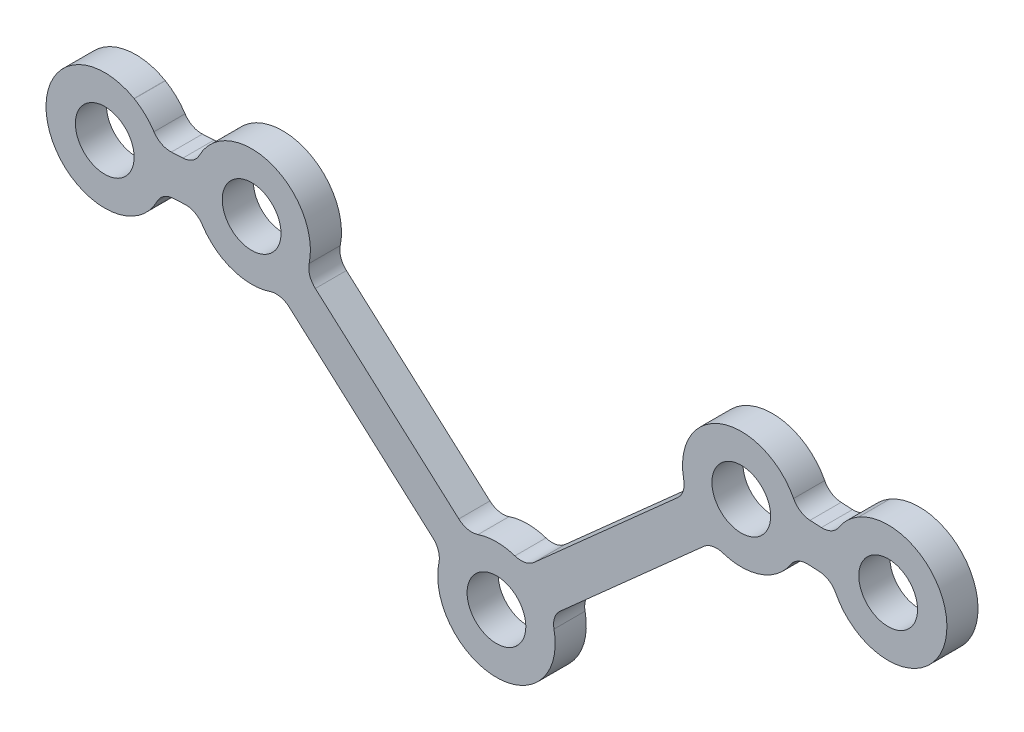
SolidWorks part; units mm, degrees
ref_plane "Front Plane" through (0, 0, 0) normal (0, 0, 1) x (1, 0, 0)
ref_plane "Top Plane" through (0, 0, 0) normal (0, 1, 0) x (1, 0, 0)
ref_plane "Right Plane" through (0, 0, 0) normal (1, 0, 0) x (0, 0, -1)
sketch "Sketch4" plane through (0, 0, 0) normal (0, 0, 1) x (1, 0, 0)
  line L0 (0, -3) -> (0, 1.5) construction
  line L6 (11, 11.1368) -> (10.9965, 11.1337)
  line L7 (-1.9217, 3.0508) -> (-9.2481, 9.5764)
  line L8 (-16.5994, 11.9343) -> (-16.0088, 11.9632)
  line L9 (-10.9965, 11.1337) -> (-11, 11.1368)
  line L10 (10.5783, 8.0829) -> (3.2519, 1.5573)
  line L11 (-3.2519, 1.5573) -> (-10.5783, 8.0829)
  line L12 (-16.4824, 9.9376) -> (-15.9111, 9.9656)
  line L13 (16.5915, 11.9257) -> (16.0107, 11.9554)
  line L16 (0, -3) -> (0, 1.5) construction
  line L19 (-10.9965, 11.1337) -> (-11, 11.1337) construction
  line L26 (10.9965, 11.1337) -> (11, 11.1337) construction
  line L27 (9.2481, 9.5764) -> (1.9217, 3.0508)
  line L28 (16.4893, 9.9283) -> (15.9085, 9.958)
  arc A0 (0.9424, 2.8481) -> (-0.9424, 2.8481) centre (0, 0) ccw
  circle A1 centre (-12.5, 11.1337) radius 1.5
  circle A2 centre (-20, 10.75) radius 1.5
  arc A3 (17.3287, 9.3847) -> (17.482, 12.3808) centre (20, 10.75) ccw
  arc A4 (-17.4862, 12.3873) -> (-17.3252, 9.3916) centre (-20, 10.75) ccw
  arc A5 (15.1713, 12.499) -> (9.5622, 10.5258) centre (12.5, 11.1337) ccw
  arc A6 (-9.5622, 10.5258) -> (-15.1683, 12.5049) centre (-12.5, 11.1337) ccw
  arc A7 (11.5576, 8.2856) -> (15.018, 9.5029) centre (12.5, 11.1337) ccw
  arc A8 (-2.9378, 0.6079) -> (2.9378, 0.6079) centre (0, 0) ccw
  arc A9 (-15.0217, 9.5085) -> (-11.5576, 8.2856) centre (-12.5, 11.1337) ccw
  arc A10 (17.482, 12.3808) -> (16.5915, 11.9257) centre (16.6426, 12.9244) cw
  arc A11 (15.1713, 12.499) -> (16.0107, 11.9554) centre (16.0618, 12.9541) ccw
  arc A12 (17.3287, 9.3847) -> (16.4893, 9.9283) centre (16.4382, 8.9296) ccw
  arc A13 (15.018, 9.5029) -> (15.9085, 9.958) centre (15.8574, 8.9593) cw
  circle A14 centre (0, 0) radius 1.5
  arc A15 (10.5783, 8.0829) -> (11.5576, 8.2856) centre (11.2435, 7.3362) cw
  arc A16 (9.2481, 9.5764) -> (9.5622, 10.5258) centre (8.583, 10.3231) ccw
  arc A17 (0.9424, 2.8481) -> (1.9217, 3.0508) centre (1.2565, 3.7975) ccw
  arc A18 (2.9378, 0.6079) -> (3.2519, 1.5573) centre (3.917, 0.8106) cw
  arc A19 (-1.9217, 3.0508) -> (-0.9424, 2.8481) centre (-1.2565, 3.7975) ccw
  arc A20 (-3.2519, 1.5573) -> (-2.9378, 0.6079) centre (-3.917, 0.8106) cw
  arc A21 (-11.5576, 8.2856) -> (-10.5783, 8.0829) centre (-11.2435, 7.3362) cw
  arc A22 (-9.2481, 9.5764) -> (-9.5622, 10.5258) centre (-8.583, 10.3231) cw
  arc A23 (-15.0217, 9.5085) -> (-15.9111, 9.9656) centre (-15.8622, 8.9668) ccw
  arc A24 (-15.1683, 12.5049) -> (-16.0088, 11.9632) centre (-16.0577, 12.962) cw
  arc A25 (-16.4824, 9.9376) -> (-17.3252, 9.3916) centre (-16.4335, 8.9388) ccw
  arc A26 (-18.5037, 13.3502) -> (-18.4928, 13.3439) centre (-17.9197, 14.3475) ccw
  arc A27 (-16.5994, 11.9343) -> (-17.4862, 12.3873) centre (-16.6483, 12.9331) cw
  circle A56 centre (12.5, 11.1337) radius 1.5
  arc A57 (-18.4928, 13.3439) -> (-18.5037, 13.3502) centre (-20, 10.75) ccw
  arc A58 (18.5037, 13.3502) -> (18.4928, 13.3439) centre (17.9197, 14.3475) cw
  circle A73 centre (20, 10.75) radius 1.5
  arc A79 (18.4928, 13.3439) -> (18.5037, 13.3502) centre (20, 10.75) cw
  point P16 (0, -7.5575)
  point P22 (11.053, 8.5057)
  point P44 (0, 8.1)
  point P50 (-2.7772, 1.1345)
  dimension "D1" = 1
  dimension "D3" = 1
  dimension "D6" = 1
  dimension "D7" = 1
  dimension "D5" = 1
  dimension "D8" = 1
  dimension "D9" = 1
  dimension "D14" = 1
  dimension "D15" = 1
  dimension "D2" = 1
  dimension "D4" = 1
  dimension "D10" = 1
  dimension "D11" = 1
  dimension "D12" = 1
  dimension "D13" = 1
  dimension "D16" = 1
extrude "Boss-Extrude2" add sketch "Sketch4" along normal blind 1.5875
sketch "Sketch5" plane through (0, 0, 1.5875) normal (0, 0, 1) x (1, 0, 0)
